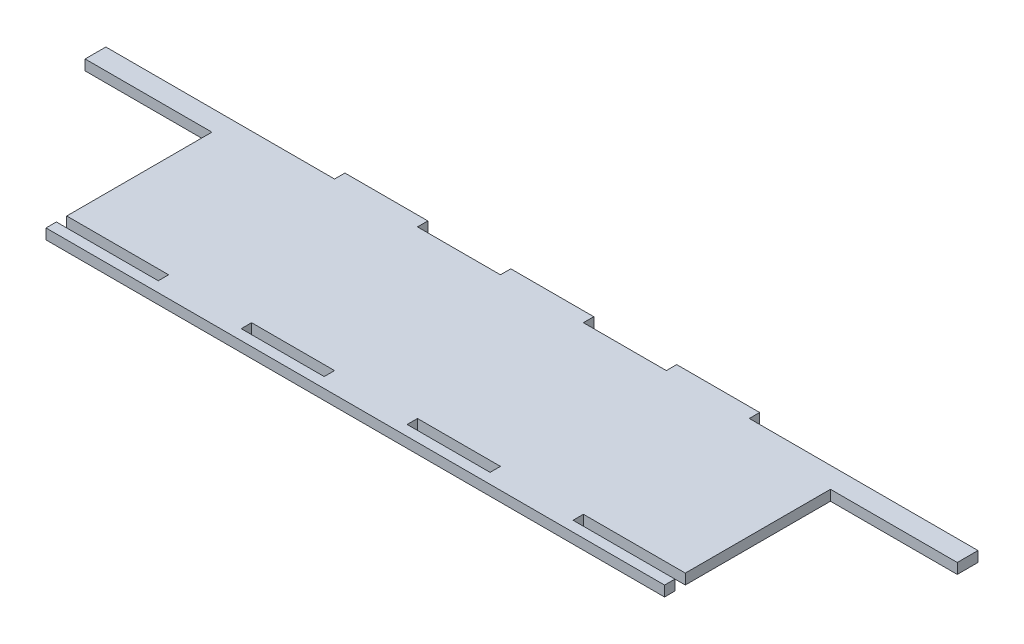
SolidWorks part; units mm, degrees
ref_plane "Front Plane" through (0, 0, 0) normal (0, 0, 1) x (1, 0, 0)
ref_plane "Top Plane" through (0, 0, 0) normal (0, 1, 0) x (1, 0, 0)
ref_plane "Right Plane" through (0, 0, 0) normal (1, 0, 0) x (0, 0, -1)
sketch "Sketch1" plane through (0, 0, 0) normal (0, 1, 0) x (1, 0, 0)
  line L0 (-133.525, 19.05) -> (-94.7, 19.05)
  line L1 (-133.525, -25.4) -> (133.525, -25.4)
  line L2 (-133.525, -25.4) -> (-133.525, 25.4)
  line L3 (-133.525, 25.4) -> (133.525, 25.4)
  line L4 (133.525, -25.4) -> (133.525, 25.4)
  line L5 (-133.525, -25.4) -> (133.525, 25.4) construction
  line L6 (-133.525, 25.4) -> (133.525, -25.4) construction
  line L7 (-94.7, 19.05) -> (-94.7, -25.4)
  line L8 (133.525, 19.05) -> (94.7, 19.05)
  line L9 (94.7, 19.05) -> (94.7, -25.4)
  line L10 (-38.1, 28.575) -> (-12.7, 28.575) construction
  line L11 (-63.5, 25.4) -> (-38.1, 25.4)
  line L12 (-63.5, 25.4) -> (-63.5, 28.575)
  line L13 (-63.5, 28.575) -> (-38.1, 28.575)
  line L14 (-38.1, 25.4) -> (-38.1, 28.575)
  line L15 (-12.7, 25.4) -> (12.7, 25.4)
  line L16 (-12.7, 25.4) -> (-12.7, 28.575)
  line L17 (-12.7, 28.575) -> (12.7, 28.575)
  line L18 (12.7, 25.4) -> (12.7, 28.575)
  line L19 (38.1, 25.4) -> (63.5, 25.4)
  line L20 (38.1, 25.4) -> (38.1, 28.575)
  line L21 (38.1, 28.575) -> (63.5, 28.575)
  line L22 (63.5, 25.4) -> (63.5, 28.575)
  line L23 (12.7, 28.575) -> (38.1, 28.575) construction
  line L24 (-38.1, -28.575) -> (-12.7, -28.575) construction
  line L25 (-63.5, -25.4) -> (-38.1, -25.4)
  line L26 (-63.5, -25.4) -> (-63.5, -28.575)
  line L27 (-63.5, -28.575) -> (-38.1, -28.575)
  line L28 (-38.1, -25.4) -> (-38.1, -28.575)
  line L29 (-12.7, -25.4) -> (12.7, -25.4)
  line L30 (-12.7, -25.4) -> (-12.7, -28.575)
  line L31 (-12.7, -28.575) -> (12.7, -28.575)
  line L32 (12.7, -25.4) -> (12.7, -28.575)
  line L33 (38.1, -25.4) -> (63.5, -25.4)
  line L34 (38.1, -25.4) -> (38.1, -28.575)
  line L35 (38.1, -28.575) -> (63.5, -28.575)
  line L36 (63.5, -25.4) -> (63.5, -28.575)
  line L37 (12.7, -28.575) -> (38.1, -28.575) construction
  line L39 (-94.7, -31.75) -> (94.7, -31.75)
  line L40 (-94.7, -31.75) -> (-94.7, -28.575)
  line L41 (-94.7, -28.575) -> (94.7, -28.575)
  line L42 (94.7, -31.75) -> (94.7, -28.575)
  point P0 (0, 0)
  point P24 (0, 28.575)
  dimension "D1" = 50.8
  dimension "D2" = 267.05
  dimension "D3" = 44.45
  dimension "D4" = 38.825
  dimension "D5" = 3.175
  dimension "D6" = 25.4
extrude "Boss-Extrude1" add sketch "Sketch1" along normal blind 3.175 contours L9 L8 L4 L3 L2 L0 L7 L1 | L39 L42 L41 L35 L31 L27 L40 | L20 L19 L22 L21 | L16 L15 L18 L17 | L12 L11 L14 L13
